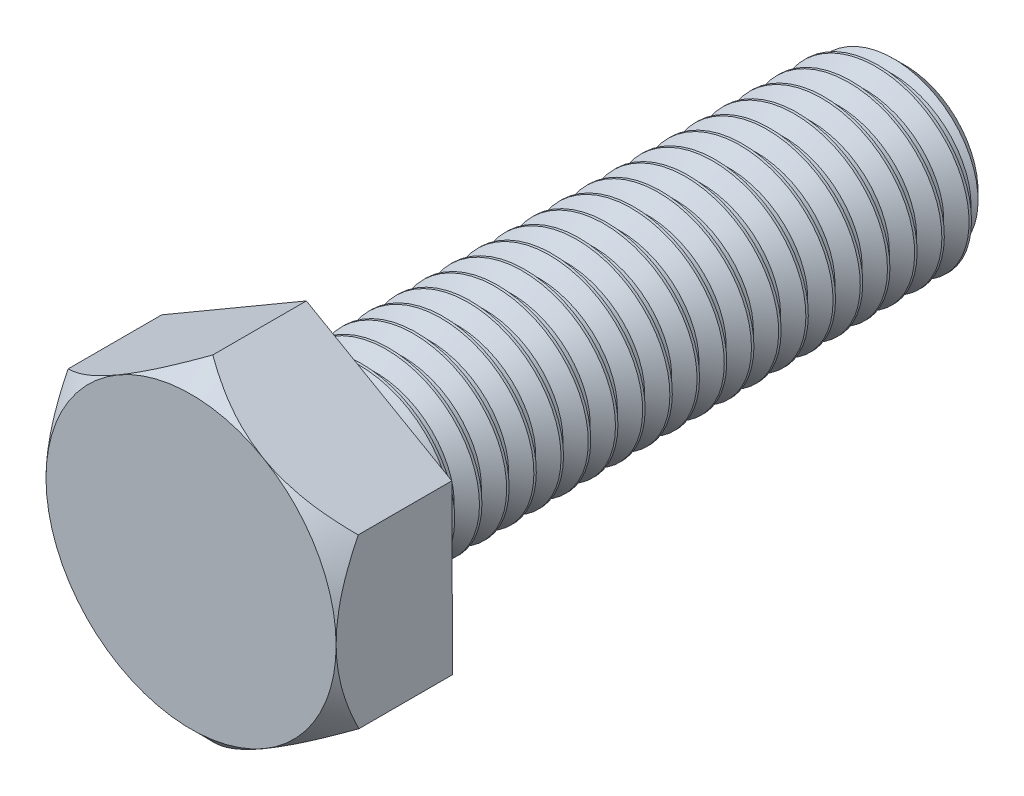
SolidWorks part; units mm, degrees
ref_plane "Front Plane" through (0, 0, 0) normal (0, 0, 1) x (1, 0, 0)
ref_plane "Top Plane" through (0, 0, 0) normal (0, 1, 0) x (1, 0, 0)
ref_plane "Right Plane" through (0, 0, 0) normal (1, 0, 0) x (0, 0, -1)
sketch "Sketch1" plane through (0, 0, 0) normal (0, 0, 1) x (1, 0, 0)
  line L1 (7.9792, 4.6546) -> (-0.0413, 9.2375)
  line L2 (-0.0413, 9.2375) -> (-8.0206, 4.583)
  line L3 (-8.0206, 4.583) -> (-7.9792, -4.6546)
  line L4 (-7.9792, -4.6546) -> (0.0413, -9.2375)
  line L5 (0.0413, -9.2375) -> (8.0206, -4.583)
  line L6 (8.0206, -4.583) -> (7.9792, 4.6546)
  circle A0 centre (0, 0) radius 8 construction
  dimension "D1" = 16
extrude "Boss-Extrude2" add sketch "Sketch1" along normal blind 6.4
sketch "Sketch2" plane through (0, 0, 0) normal (0, 0, -1) x (-1, 0, 0)
  circle A0 centre (0, 0) radius 5
extrude "Boss-Extrude3" add sketch "Sketch2" along normal blind 33
sketch "Sketch7" plane through (0, 0, -33) normal (0, 0, -1) x (-1, 0, 0)
  circle A0 centre (0, 0) radius 5
curve "Helix/Spiral1" pitch 1.5 height 31.5 turns 21
sketch "Sketch8" plane through (0, 0, -33) normal (0, 0, -1) x (-1, 0, 0)
  circle A0 centre (0, 0) radius 5 construction
  point P0 (5, 0)
sketch "Sketch9" plane through (0, 0, 0) normal (0, 1, 0) x (1, 0, 0)
  line L0 (-4.2374, 33.1181) -> (-4.2374, 32.6674)
  line L1 (-4.2374, 33.1181) -> (-5.402, 34.0824)
  line L2 (-5.402, 34.0824) -> (-5.7364, 32.1106)
  line L3 (-5.7364, 32.1106) -> (-4.2374, 32.6674)
  circle A0 centre (-5, 33) radius 0.5774 construction
chamfer "Chamfer1" distance 1 angle 45 1 edges at (-5, 0, -33)
sweep "Cut-Sweep4" cut profiles "Sketch9" path "Helix/Spiral1"
sketch "Sketch10" plane through (0, 0, 6.4) normal (0, 0, 1) x (1, 0, 0)
  line L1 (-0.0413, 9.2375) -> (-8.0206, 4.583)
  line L2 (-8.0206, 4.583) -> (-7.9792, -4.6546)
  line L3 (-7.9792, -4.6546) -> (0.0413, -9.2375)
  line L4 (0.0413, -9.2375) -> (8.0206, -4.583)
  line L5 (8.0206, -4.583) -> (7.9792, 4.6546)
  line L6 (7.9792, 4.6546) -> (-0.0413, 9.2375)
  circle A0 centre (0, 0) radius 8
  circle A1 centre (0, 0) radius 8 construction
  line M5 (-8.0206, 4.583) -> (-7.9792, -4.6546)
extrude "Cut-Extrude2" cut sketch "Sketch10" against normal blind 10 draft 45 flip side to cut contours A0 M5
